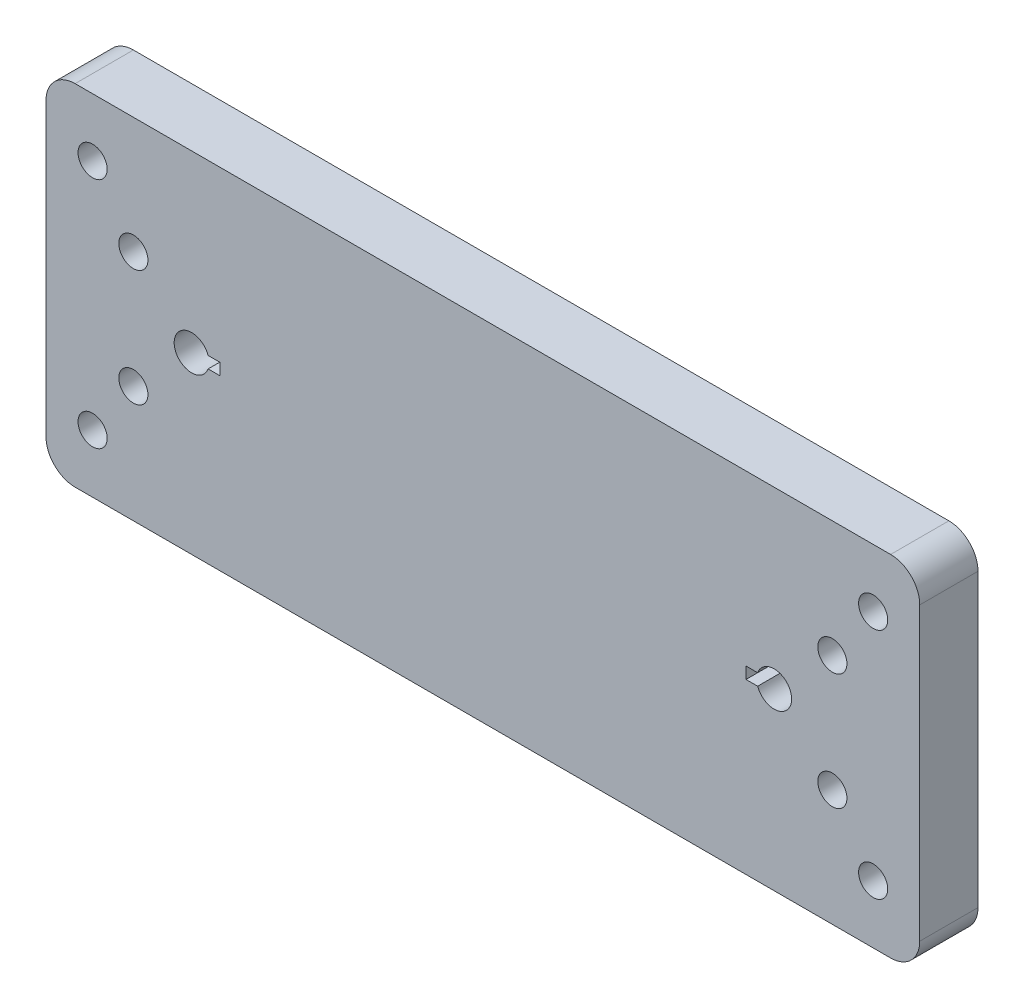
SolidWorks part; units mm, degrees
ref_plane "Front Plane" through (0, 0, 0) normal (0, 0, 1) x (1, 0, 0)
ref_plane "Top Plane" through (0, 0, 0) normal (0, 1, 0) x (1, 0, 0)
ref_plane "Right Plane" through (0, 0, 0) normal (1, 0, 0) x (0, 0, -1)
sketch "Sketch1" plane through (0, 0, 0) normal (0, 0, 1) x (1, 0, 0)
  line L1 (5, 0) -> (145, 0)
  line L2 (0, 5) -> (0, 55)
  line L3 (5, 60) -> (145, 60)
  line L4 (150, 5) -> (150, 55)
  line L5 (27.8284, 31) -> (29.8284, 31)
  line L7 (27.8284, 29) -> (29.8284, 29)
  line L8 (29.8284, 31) -> (29.8284, 29)
  line L9 (122.1716, 31) -> (120.1716, 31)
  line L11 (122.1716, 29) -> (120.1716, 29)
  line L12 (120.1716, 31) -> (120.1716, 29)
  arc A0 (145, 0) -> (150, 5) centre (145, 5) ccw
  arc A1 (145, 60) -> (150, 55) centre (145, 55) cw
  arc A2 (5, 0) -> (0, 5) centre (5, 5) cw
  arc A3 (0, 55) -> (5, 60) centre (5, 55) cw
  arc A4 (27.8284, 31) -> (27.8284, 29) centre (25, 30) ccw
  arc A5 (122.1716, 29) -> (122.1716, 31) centre (125, 30) ccw
  point P9 (150, 60)
  point P12 (0, 0)
  point P15 (0, 60)
  dimension "D3" = 5
  dimension "D4" = 6
  dimension "D5" = 100
  dimension "D6" = 25
  dimension "D7" = 30
  dimension "D1" = 60
  dimension "D2" = 150
  dimension "D8" = 2
  dimension "D9" = 2
  dimension "D10" = 1
extrude "Boss-Extrude1" add sketch "Sketch1" along normal blind 10
sketch "Sketch2" plane through (0, 0, 10) normal (0, 0, 1) x (1, 0, 0)
  line L1 (15, 40) -> (135, 40) construction
  line L2 (15, 40) -> (15, 20) construction
  line L3 (15, 20) -> (135, 20) construction
  line L4 (135, 40) -> (135, 20) construction
  circle A0 centre (15, 40) radius 2.5
  circle A1 centre (15, 20) radius 2.5
  circle A2 centre (135, 40) radius 2.5
  circle A3 centre (135, 20) radius 2.5
  arc A4 (27.8284, 31) -> (27.8284, 29) centre (25, 30) ccw construction
  arc A5 (122.1716, 29) -> (122.1716, 31) centre (125, 30) ccw construction
  dimension "D1" = 5
  dimension "D4" = 10
  dimension "D5" = 10
  dimension "D2" = 20
  dimension "D3" = 10
extrude "Cut-Extrude1" cut sketch "Sketch2" against normal through all
sketch "Sketch3" plane through (0, 0, 10) normal (0, 0, 1) x (1, 0, 0)
  line L1 (8, 50) -> (142, 50) construction
  line L2 (8, 50) -> (8, 10) construction
  line L3 (8, 10) -> (142, 10) construction
  line L4 (142, 50) -> (142, 10) construction
  circle A0 centre (8, 50) radius 2.5
  circle A1 centre (8, 10) radius 2.5
  circle A2 centre (142, 50) radius 2.5
  circle A3 centre (142, 10) radius 2.5
  arc A4 (27.8284, 31) -> (27.8284, 29) centre (25, 30) ccw construction
  circle A5 centre (15, 40) radius 2.5 construction
  circle A6 centre (135, 40) radius 2.5 construction
  dimension "D1" = 5
  dimension "D5" = 7
  dimension "D2" = 20
  dimension "D3" = 40
  dimension "D4" = 7
extrude "Cut-Extrude3" cut sketch "Sketch3" against normal through all
